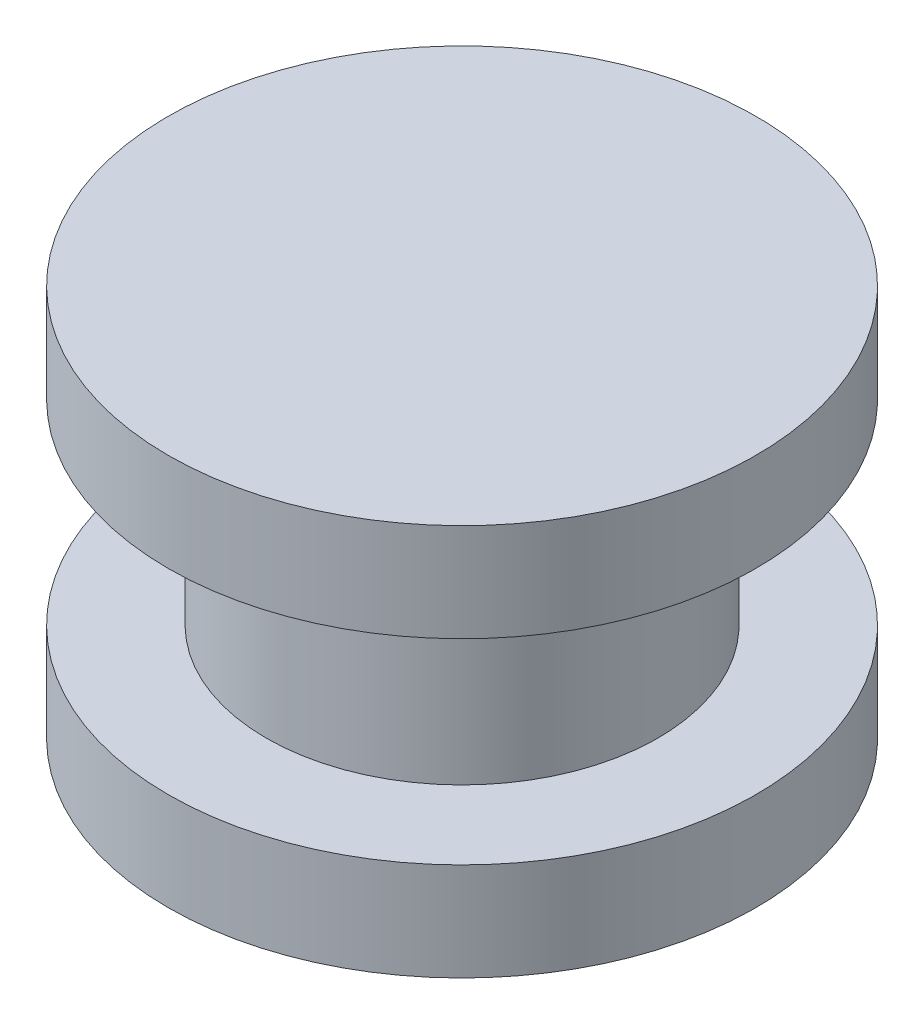
SolidWorks part; units mm, degrees
ref_plane "Front Plane" through (0, 0, 0) normal (0, 0, 1) x (1, 0, 0)
ref_plane "Top Plane" through (0, 0, 0) normal (0, 1, 0) x (1, 0, 0)
ref_plane "Right Plane" through (0, 0, 0) normal (1, 0, 0) x (0, 0, -1)
sketch "Sketch1" plane through (0, 0, 0) normal (0, 1, 0) x (1, 0, 0)
  circle A0 centre (0, 0) radius 3
extrude "Boss-Extrude1" add sketch "Sketch1" along normal blind 1
sketch "Sketch2" plane through (0, 1, 0) normal (0, 1, 0) x (1, 0, 0)
  circle A0 centre (0, 0) radius 2
extrude "Boss-Extrude2" add sketch "Sketch2" along normal blind 2
sketch "Sketch3" plane through (0, 3, 0) normal (0, 1, 0) x (1, 0, 0)
  circle A0 centre (0, 0) radius 3
extrude "Boss-Extrude3" add sketch "Sketch3" along normal blind 1
